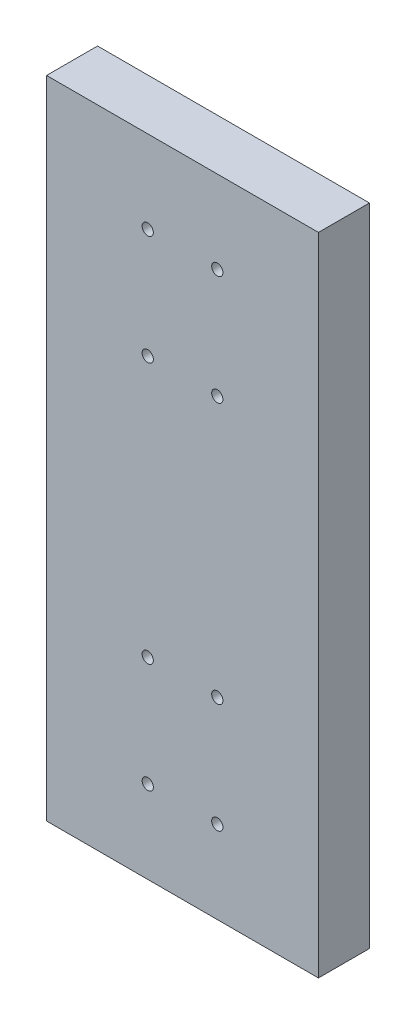
SolidWorks part; units mm, degrees
material "Delrin 2700 NC010, Low Viscosity Acetal Copolymer (SS)"
ref_plane "Front Plane" through (0, 0, 0) normal (0, 0, 1) x (1, 0, 0)
ref_plane "Top Plane" through (0, 0, 0) normal (0, 1, 0) x (1, 0, 0)
ref_plane "Right Plane" through (0, 0, 0) normal (1, 0, 0) x (0, 0, -1)
sketch "Sketch1" plane through (0, 4848.8359, 0) normal (0, 0, 1) x (1, 0, 0)
  line L1 (-421.4245, 136.0597) -> (-319.8245, 136.0597)
  line L2 (-421.4245, 136.0597) -> (-421.4245, -105.2403)
  line L3 (-421.4245, -105.2403) -> (-319.8245, -105.2403)
  line L4 (-366.179, 132.0441) -> (-375.07, 132.0441)
  line L5 (-408.0436, -99.7403) -> (-389.0097, -104.8134)
  line L6 (-381.1959, -98.1258) -> (-360.0531, -98.1258)
  line L7 (-352.2392, -104.8134) -> (-333.2054, -99.7403)
  line L8 (-366.179, 132.0441) -> (-375.07, 132.0441) construction
  line L9 (-408.0436, -99.7403) -> (-389.0097, -104.8134) construction
  line L10 (-381.1959, -98.1258) -> (-360.0531, -98.1258) construction
  line L11 (-352.2392, -104.8134) -> (-333.2054, -99.7403) construction
  line L12 (-319.8245, 136.0597) -> (-319.8245, -105.2403)
  spline S6 degree 3 poles (1642.8394, -4438.5006) (-286.2821, 176.546) (-376.6001, 150.0349) (-379.443, 124.4113) (-381.0748, 120.1436) (-384.6128, 117.4799) (-387.7595, 115.4802) (-392.547, 109.8) (-395.7298, 101.6251) (-401.1741, 88.6994) (-406.5846, 72.375) (-415.3628, 43.2675) (-467.623, -325.7387) (16.788, -704.583) (-5294.3657, -741.6774) knots -0.274894 -0.274894 -0.274894 -0.274894 0.022097 0.039559 0.063259 0.077264 0.095563 0.110967 0.171488 0.206517 0.29131 0.391743 0.596457 5.044089 5.044089 5.044089 5.044089 only from (-375.07, 132.0441) to (-419.7016, -90.6908)
  spline S7 degree 3 poles (4544.1896, 491.219) (-5525.8194, -458.1188) (4710.0194, 96.5851) (-5406.7565, -187.2843) knots -5.429645 -5.429645 -5.429645 -5.429645 6.566821 6.566821 6.566821 6.566821 only from (-419.7016, -90.6908) to (-408.0436, -99.7403)
  spline S8 degree 3 poles (-4069.4144, 3279.1211) (3304.9216, -3542.8961) (-4098.274, 3310.4514) (3374.8028, -3397.3059) knots -5.129626 -5.129626 -5.129626 -5.129626 6.248147 6.248147 6.248147 6.248147 only from (-389.0097, -104.8134) to (-381.1959, -98.1258)
  spline S9 degree 3 poles (-4116.0535, -3397.3074) (3357.0624, 3310.4849) (-4046.2429, -3542.963) (3328.2726, 3279.2202) knots -5.248148 -5.248148 -5.248148 -5.248148 6.129681 6.129681 6.129681 6.129681 only from (-360.0531, -98.1258) to (-352.2392, -104.8134)
  spline S10 degree 3 poles (4665.5712, -187.2861) (-5451.3484, 96.5884) (4784.6666, -458.1248) (-5285.5493, 491.2295) knots -5.566846 -5.566846 -5.566846 -5.566846 6.429689 6.429689 6.429689 6.429689 only from (-333.2054, -99.7403) to (-321.5474, -90.6908)
  spline S11 degree 3 poles (4553.1165, -741.6774) (-758.037, -704.583) (-273.626, -325.7387) (-325.8862, 43.2675) (-334.6644, 72.375) (-340.0749, 88.6994) (-345.5191, 101.6251) (-348.702, 109.8) (-353.4894, 115.4802) (-356.6361, 117.4799) (-360.1742, 120.1436) (-361.806, 124.4113) (-364.6487, 150.0329) (-454.9513, 176.5415) (-2383.5597, -4437.2359) knots -4.044089 -4.044089 -4.044089 -4.044089 0.403543 0.608257 0.70869 0.793483 0.828512 0.889033 0.904437 0.922736 0.936741 0.960441 0.977903 1.274867 1.274867 1.274867 1.274867 only from (-321.5474, -90.6908) to (-366.179, 132.0441)
  spline S12 degree 3 poles (-375.07, 132.0441) (-377.191, 132.2448) (-378.9111, 129.2047) (-379.443, 124.4113) (-381.0748, 120.1436) (-384.6128, 117.4799) (-387.7595, 115.4802) (-392.547, 109.8) (-395.7298, 101.6251) (-401.1741, 88.6994) (-406.5846, 72.375) (-415.3628, 43.2675) (-423.1553, -11.7552) (-420.6889, -59.2818) (-419.7016, -90.6908) knots 0 0 0 0 0.022097 0.039559 0.063259 0.077264 0.095563 0.110967 0.171488 0.206517 0.29131 0.391743 0.596457 1 1 1 1 construction
  spline S13 degree 3 poles (-419.7016, -90.6908) (-421.1934, -96.3385) (-409.4574, -98.9028) (-408.0436, -99.7403) knots 0 0 0 0 1 1 1 1 construction
  spline S14 degree 3 poles (-389.0097, -104.8134) (-382.2379, -107.2033) (-386.3443, -98.8102) (-381.1959, -98.1258) knots 0 0 0 0 1 1 1 1 construction
  spline S15 degree 3 poles (-360.0531, -98.1258) (-354.9047, -98.8102) (-359.0111, -107.2033) (-352.2392, -104.8134) knots 0 0 0 0 1 1 1 1 construction
  spline S16 degree 3 poles (-333.2054, -99.7403) (-331.7916, -98.9028) (-320.0556, -96.3385) (-321.5474, -90.6908) knots 0 0 0 0 1 1 1 1 construction
  spline S17 degree 3 poles (-321.5474, -90.6908) (-320.5601, -59.2818) (-318.0936, -11.7552) (-325.8862, 43.2675) (-334.6644, 72.375) (-340.0749, 88.6994) (-345.5191, 101.6251) (-348.702, 109.8) (-353.4894, 115.4802) (-356.6361, 117.4799) (-360.1742, 120.1436) (-361.806, 124.4113) (-362.3378, 129.2047) (-364.058, 132.2448) (-366.179, 132.0441) knots 0 0 0 0 0.403543 0.608257 0.70869 0.793483 0.828512 0.889033 0.904437 0.922736 0.936741 0.960441 0.977903 1 1 1 1 construction
  point P10 (-370.6245, 136.0597)
  point P12 (-370.6245, 132.0441)
  dimension "D2" = 101.6
  dimension "D3" = 241.3
  dimension "D1" = 0
extrude "Boss-Extrude1" add sketch "Sketch1" along normal blind 19.05
hole_wizard "Tap Drill for M4 Helicoil0" positions "Sketch2" profile "Sketch3" hole size "M4x0.7" standard "ANSI Metric"
sketch "Sketch2" plane through (0, 0, 19.05) normal (0, 0, 1) x (-1, 0, 0)
  point P0 (383.6245, -4912.9956)
  point P3 (357.6245, -4912.9956)
  point P6 (357.6245, -4953.9956)
  point P9 (383.6245, -4953.9956)
  point P12 (383.6245, -4774.4956)
  point P15 (383.6245, -4815.4956)
  point P18 (357.6245, -4815.4956)
  point P21 (357.6245, -4774.4956)
sketch "Sketch3" plane through (-383.6245, 4912.9956, 19.05) normal (1, 0, 0) x (0, -1, 0)
  line L0 (0, 0) -> (0, 12.6618)
  line L1 (0, 12.6618) -> (2.1, 11.4)
  line L2 (2.1, 11.4) -> (2.1, 0)
  line L5 (2.1, 0) -> (0, 0)
  line L10 (0, 12.6618) -> (-2.1, 11.4) construction
  line L11 (0, -6.35) -> (0, 107.95) construction
  dimension "Hole Dia." = 4.2
  dimension "Hole Depth" = 11.4
  dimension "Drill Angle" = 118
